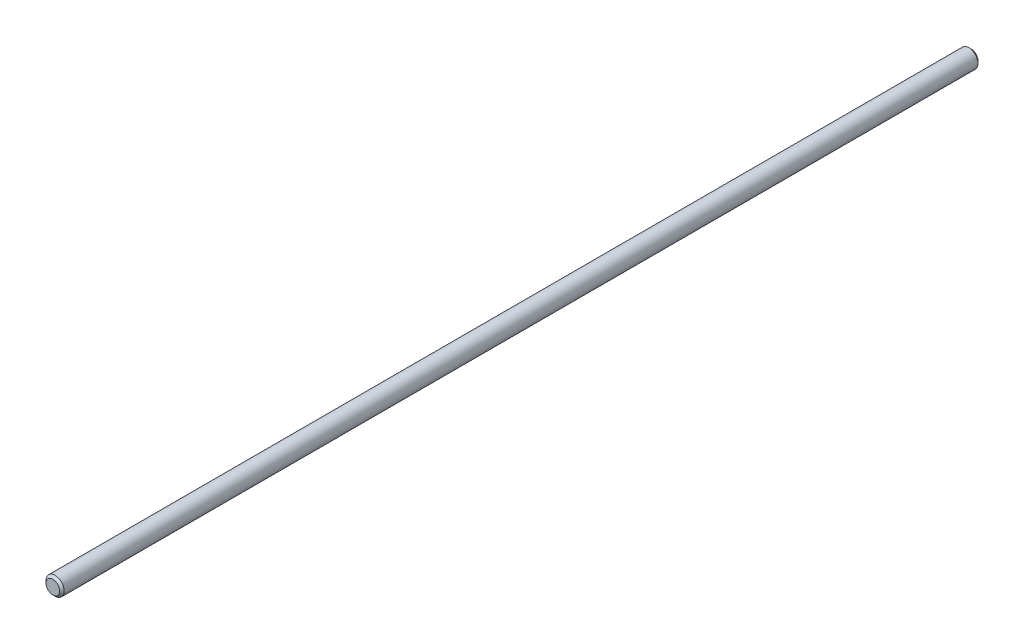
SolidWorks part; units mm, degrees
material "1060 Alloy"
ref_plane "Front" through (0, 0, 0) normal (0, 0, 1) x (1, 0, 0)
ref_plane "Top" through (0, 0, 0) normal (0, 1, 0) x (1, 0, 0)
ref_plane "Right" through (0, 0, 0) normal (1, 0, 0) x (0, 0, -1)
sketch "Sketch1" plane through (0, 0, 0) normal (0, 0, 1) x (1, 0, 0)
  circle A0 centre (0, 0) radius 4
  dimension "D1" = 8
extrude "Boss-Extrude1" add sketch "Sketch1" along normal blind 405
chamfer "Chamfer2" distance 1 angle 45 1 edges at (4, 0, 0)
chamfer "Chamfer3" distance 1 angle 45 1 edges at (4, 0, 405)
